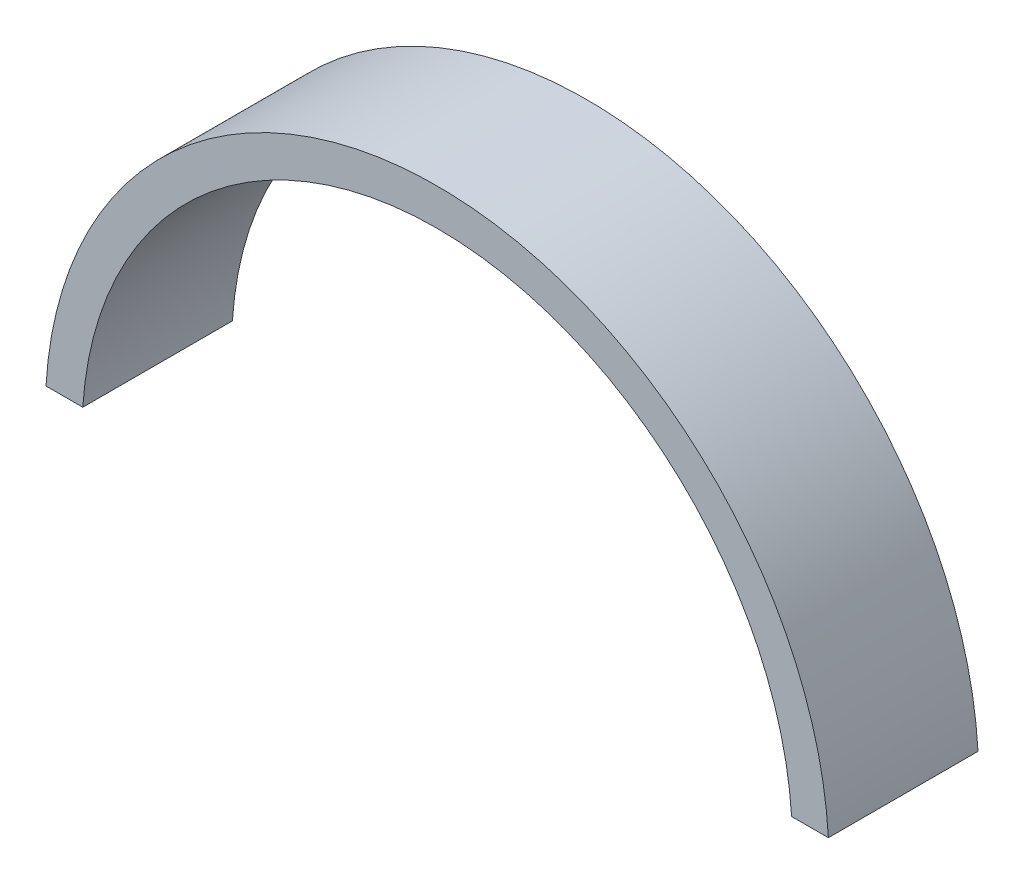
SolidWorks part; units mm, degrees
ref_plane "Front Plane" through (0, 0, 0) normal (0, 0, 1) x (1, 0, 0)
ref_plane "Top Plane" through (0, 0, 0) normal (0, 1, 0) x (1, 0, 0)
ref_plane "Right Plane" through (0, 0, 0) normal (1, 0, 0) x (0, 0, -1)
sketch "Sketch1" plane through (0, 0, 0) normal (0, 0, 1) x (1, 0, 0)
  line L0 (-90.1815, 4.6108) -> (-71.0625, 4.6108)
  line L3 (71.0625, 4.6108) -> (90.1815, 4.6108)
  arc A0 (90.1815, 4.6108) -> (-90.1815, 4.6108) centre (0, 0) ccw
  arc A1 (71.0625, 4.6108) -> (-71.0625, 4.6108) centre (0, 0) ccw
  arc A4 (78.438, 4.6108) -> (-78.438, 4.6108) centre (0, 0) ccw
  point P5 (0, 0)
  point P10 (-78.438, 4.6108)
  point P11 (-71.0625, 4.6108)
  point P13 (71.0625, 4.6108)
  point P14 (78.438, 4.6108)
  point P15 (-71.0625, 4.6108)
  point P16 (-78.438, 4.6108)
  point P17 (71.0625, 4.6108)
  point P18 (78.438, 4.6108)
extrude "Boss-Extrude1" add sketch "Sketch1" along normal blind 30 contours L3 A4 L0 A1
sketch3d "3DSketch1"
  line L0 (-78.438, 4.6108, 15) -> (78.438, 4.6108, 15)
  line L1 (-78.438, 4.6108, 30) -> (-78.438, 4.6108, 0) construction
  line L2 (78.438, 4.6108, 30) -> (78.438, 4.6108, 0) construction
  point P6 (-47.062, 4.6108, 15)
  point P7 (-15.262, 4.6108, 15)
  point P8 (16.538, 4.6108, 15)
  point P9 (48.338, 4.6108, 15)
  point P10 (-78.438, 4.6108, 15)
  point P11 (0, 0, 0)
  dimension "D1" = 31.376
  dimension "D2" = 156.876
  dimension "D3" = 31.8
  dimension "D4" = 31.8
  dimension "D5" = 31.8
  dimension "D6" = 30.1
